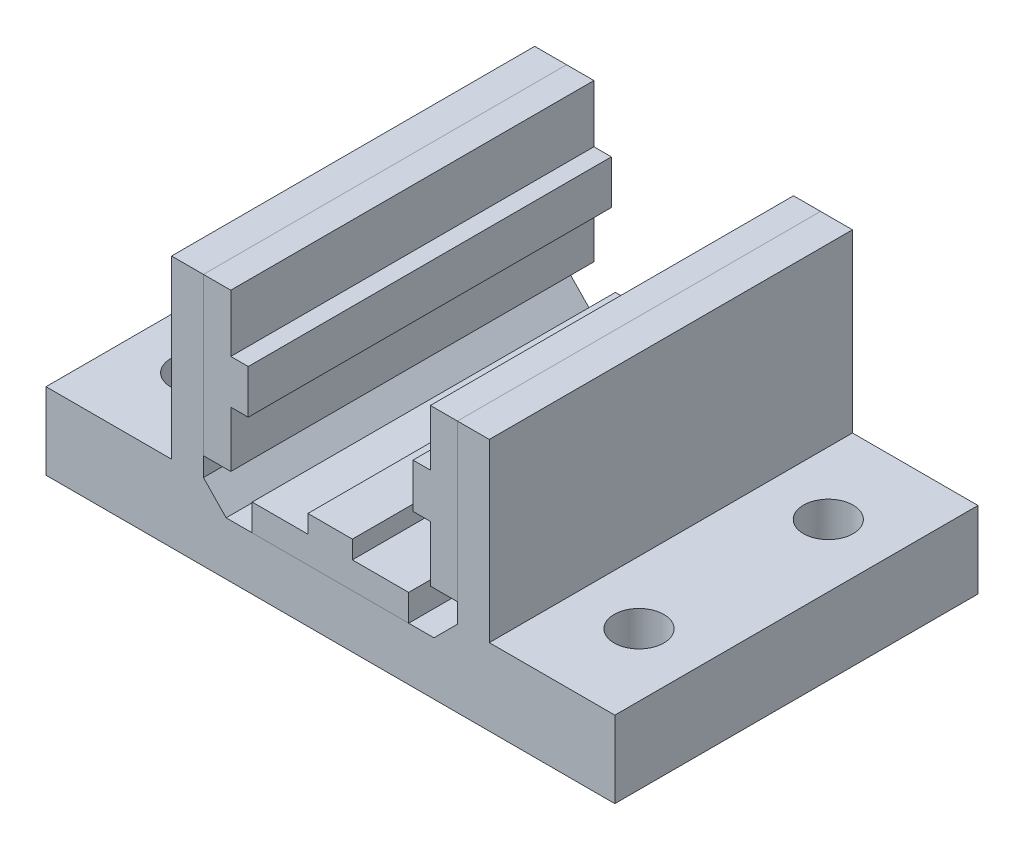
SolidWorks part; units mm, degrees
ref_plane "Front Plane" through (0, 0, 0) normal (0, 0, 1) x (1, 0, 0)
ref_plane "Top Plane" through (0, 0, 0) normal (0, 1, 0) x (1, 0, 0)
ref_plane "Right Plane" through (0, 0, 0) normal (1, 0, 0) x (0, 0, -1)
sketch "Sketch1" plane through (0, 0, 0) normal (0, 0, 1) x (1, 0, 0)
  line L0 (-22.2013, -33.2232) -> (52.6017, -33.2232)
  line L1 (52.6017, -33.2232) -> (52.6017, -23.1394)
  line L3 (31.9007, -23.1394) -> (31.9007, 0)
  line L4 (31.9007, 0) -> (36.0917, 0)
  line L5 (36.0917, 0) -> (36.0917, -23.1394)
  line L6 (36.0917, -23.1394) -> (52.6017, -23.1394)
  line L7 (-1.5003, -23.1394) -> (-1.5003, 0)
  line L8 (-1.5003, 0) -> (-5.6913, 0)
  line L9 (-5.6913, 0) -> (-5.6913, -23.1394)
  line L10 (-5.6913, -23.1394) -> (-22.2013, -23.1394)
  line L11 (-22.2013, -23.1394) -> (-22.2013, -33.2232)
  line L12 (-1.5003, -23.1394) -> (1.486, -26.2283)
  line L13 (1.486, -26.2283) -> (28.8118, -26.2283)
  line L14 (28.8118, -26.2283) -> (31.9007, -23.1394)
extrude "Boss-Extrude1" add sketch "Sketch1" along normal blind 47.752
sketch "Sketch2" plane through (0, 0, 0) normal (0, 0, -1) x (-1, 0, 0)
  line L0 (-31.9007, 0) -> (-28.3447, 0)
  line L2 (-28.3447, 0) -> (-28.3447, -7.366)
  line L3 (-28.3447, -7.366) -> (-26.0587, -7.366)
  line L4 (-26.0587, -7.366) -> (-26.0587, -13.208)
  line L5 (-26.0587, -13.208) -> (-28.3447, -13.208)
  line L6 (-28.3447, -13.208) -> (-28.3447, -20.574)
  line L7 (-28.3447, -20.574) -> (-31.9007, -20.574)
  line L8 (-31.9007, -20.574) -> (-31.9007, 0)
  line L9 (-36.0917, 0) -> (-31.9007, 0) construction
extrude "Boss-Extrude2" add sketch "Sketch2" against normal blind 47.752 separate body
sketch "Sketch4" plane through (0, 0, 47.752) normal (0, 0, 1) x (1, 0, 0)
  line L0 (-1.5003, 0) -> (-1.5003, -20.6459)
  line L1 (-1.5003, -23.1394) -> (-1.5003, 0) construction
  line L2 (-1.5003, -20.6459) -> (2.0979, -20.6459)
  line L3 (2.0979, -20.6459) -> (2.0979, -13.3175)
  line L4 (2.0979, -13.3175) -> (4.3927, -13.3175)
  line L5 (4.3927, -13.3175) -> (4.3927, -7.5436)
  line L6 (4.3927, -7.5436) -> (2.0979, -7.5436)
  line L7 (2.0979, -7.5436) -> (2.0979, 0)
  line L8 (2.0979, 0) -> (-1.5003, 0)
extrude "Boss-Extrude3" add sketch "Sketch4" against normal blind 47.752 separate body
sketch "Sketch5" plane through (0, 0, 47.752) normal (0, 0, 1) x (1, 0, 0)
  line L3 (28.8118, -26.2283) -> (1.486, -26.2283) construction
  line L4 (4.915, -26.2283) -> (25.489, -26.2283)
  line L5 (25.489, -26.2283) -> (25.489, -22.7186)
  line L6 (25.489, -22.7186) -> (18.0871, -22.7186)
  line L7 (18.0871, -22.7186) -> (18.0871, -20.3498)
  line L8 (18.0871, -20.3498) -> (12.2392, -20.3498)
  line L9 (12.2392, -20.3498) -> (12.2392, -22.7186)
  line L10 (12.2392, -22.7186) -> (4.915, -22.7186)
  line L11 (4.915, -22.7186) -> (4.915, -26.2283)
extrude "Boss-Extrude4" add sketch "Sketch5" against normal blind 47.752 separate body
sketch "Sketch8" plane through (0, -23.1394, 0) normal (0, 1, 0) x (-1, 0, 0)
  line L2 (-52.6017, 47.752) -> (-52.6017, 0) construction
  line L4 (-52.6017, 0) -> (-36.0917, 0) construction
  line L5 (-52.6017, 47.752) -> (-36.0917, 47.752) construction
  line L6 (5.6913, 0) -> (22.2013, 0) construction
  line L7 (5.6913, 47.752) -> (22.2013, 47.752) construction
  line L8 (22.2013, 47.752) -> (22.2013, 0) construction
  circle A0 centre (13.9463, 11.43) radius 3.2639
  circle A1 centre (13.9463, 36.322) radius 3.2639
  circle A2 centre (-44.3467, 11.43) radius 3.2639
  circle A3 centre (-44.3467, 36.322) radius 3.2639
  point P16 (13.9463, 47.752)
  dimension "D1" = 8.255
  dimension "D7" = 6.5278
  dimension "D2" = 11.43
  dimension "D3" = 11.43
  dimension "D4" = 11.43
  dimension "D5" = 11.43
  dimension "D6" = 8.255
extrude "Cut-Extrude1" cut sketch "Sketch8" against normal blind 127
